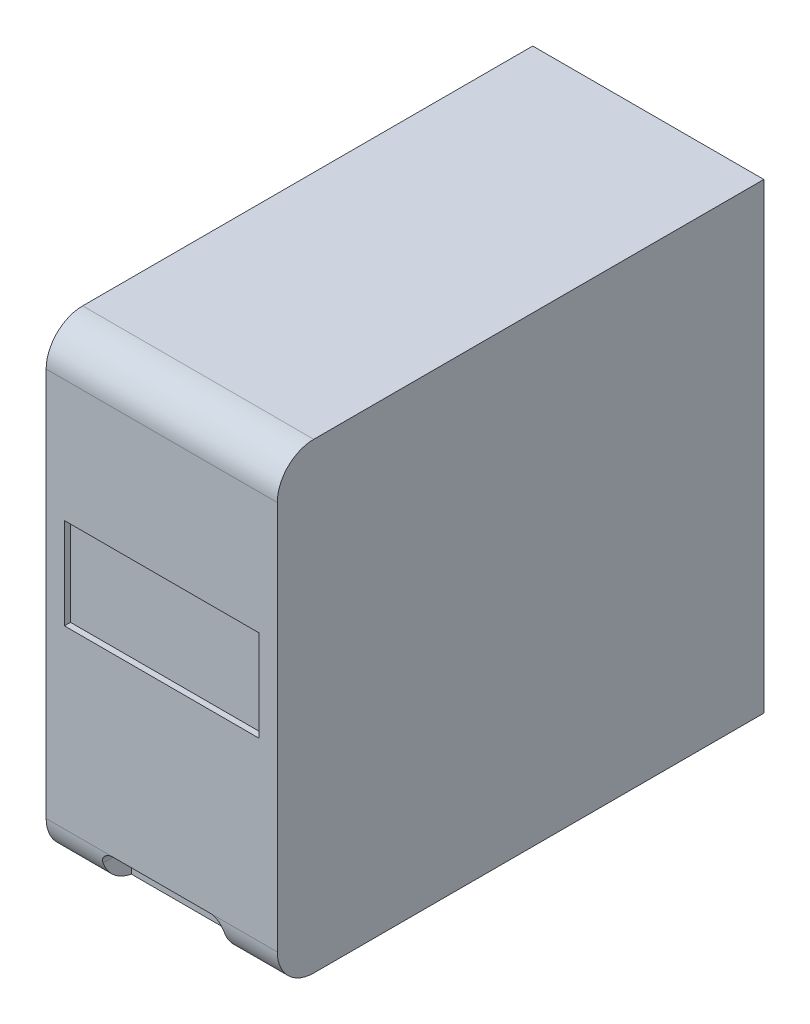
SolidWorks part; units mm, degrees
ref_plane "Front Plane" through (0, 0, 0) normal (0, 0, 1) x (1, 0, 0)
ref_plane "Top Plane" through (0, 0, 0) normal (0, 1, 0) x (1, 0, 0)
ref_plane "Right Plane" through (0, 0, 0) normal (1, 0, 0) x (0, 0, -1)
sketch "Croquis1" plane through (0, 0, 0) normal (1, 0, 0) x (0, 0, -1)
  line L1 (200, -190) -> (-200, -190)
  line L2 (200, -190) -> (200, 190)
  line L3 (200, 190) -> (-200, 190)
  line L4 (-200, -190) -> (-200, 190)
  line L5 (200, -190) -> (-200, 190) construction
  line L6 (200, 190) -> (-200, -190) construction
  point P0 (0, 0)
  dimension "D1" = 400
  dimension "D2" = 380
extrude "Saliente-Extruir1" add sketch "Croquis1" along normal mid plane 190
fillet "Redondeo1" radius 30 2 edges at (0, -190, 200) (0, 190, 200)
sketch "Croquis2" plane through (0, 0, 200) normal (0, 0, 1) x (1, 0, 0)
  line L0 (95, 160) -> (-95, 160) construction
  line L1 (95, 160) -> (-95, 160)
  line L2 (95, 160) -> (95, 59.672) construction
  line L3 (95, 160) -> (95, -160) construction
  line L6 (-95, 160) -> (-95, -160) construction
  line L7 (-95, -57.2691) -> (-95, 59.672)
  line L9 (95, 59.672) -> (80, 59.672) construction
  line L10 (-80, 59.672) -> (-95, 59.672) construction
  line L11 (80, 59.672) -> (-80, 59.672)
  line L12 (80, 59.672) -> (80, -15.328)
  line L13 (80, -15.328) -> (-80, -15.328)
  line L14 (-80, 59.672) -> (-80, -15.328)
  dimension "D1" = 75
  dimension "D2" = 15
extrude "Cortar-Extruir1" cut sketch "Croquis2" against normal blind 5 contours L11 L14 L13 L12
sketch "Croquis3" plane through (0, 0, 200) normal (0, 0, 1) x (1, 0, 0)
  line L0 (0, 0) -> (0, -160) construction
  line L1 (-95, -160) -> (95, -160) construction
  line L2 (40, -160) -> (-40, -160)
  line L3 (-50, -170) -> (-50, -190)
  line L4 (95, -190) -> (-95, -190) construction
  line L5 (-50, -190) -> (50, -190)
  line L6 (50, -190) -> (50, -170)
  arc A0 (50, -170) -> (40, -160) centre (40, -170) ccw
  arc A1 (-40, -160) -> (-50, -170) centre (-40, -170) ccw
  point P8 (0, -160)
  point P14 (50, -160)
  point P17 (-50, -160)
  dimension "D2" = 10
  dimension "D1" = 100
extrude "Cortar-Extruir2" cut sketch "Croquis3" against normal blind 25 contours L6 A0 L2 A1 L3 L5
equation "\"D1@Saliente-Extruir1\"=190"
